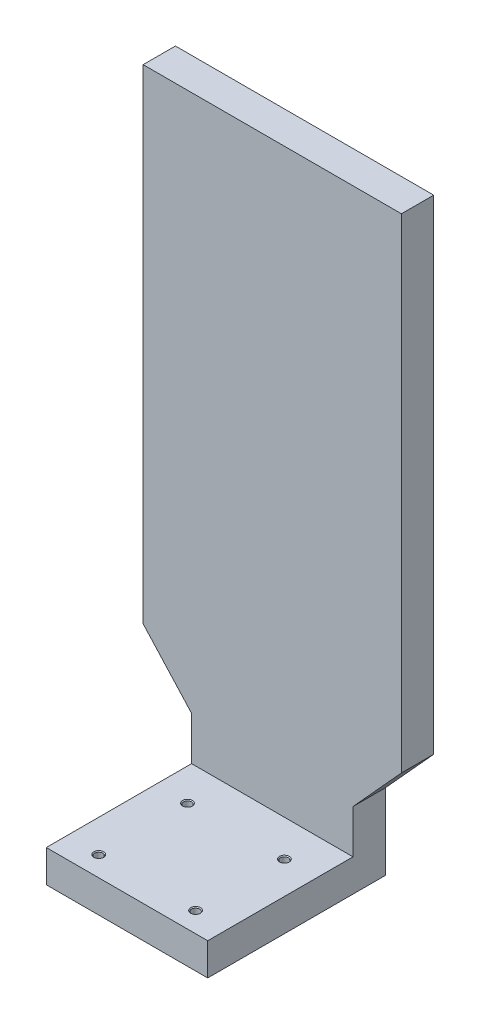
SolidWorks part; units mm, degrees
material "Aluminium"
ref_plane "Ebene vorne" through (0, 0, 0) normal (0, 0, 1) x (1, 0, 0)
ref_plane "Ebene oben" through (0, 0, 0) normal (0, 1, 0) x (1, 0, 0)
ref_plane "Ebene rechts" through (0, 0, 0) normal (1, 0, 0) x (0, 0, -1)
sketch "Skizze1" plane through (0, 0, 0) normal (0, 0, 1) x (1, 0, 0)
  line L0 (80, 0) -> (80, 300) construction
  line L1 (0, 0) -> (160, 0)
  line L2 (0, 0) -> (0, 300)
  line L3 (0, 300) -> (160, 300)
  line L4 (160, 0) -> (160, 300)
  line L5 (80, -33) -> (80, -60) construction
  line L6 (130, -33) -> (160, 0)
  line L7 (30, -33) -> (130, -33)
  line L8 (30, -33) -> (30, -60)
  line L9 (30, -60) -> (130, -60)
  line L10 (130, -33) -> (130, -60)
  line L11 (0, 0) -> (30, -33)
  dimension "D1" = 160
  dimension "D2" = 300
  dimension "D3" = 360
  dimension "D4" = 27
  dimension "D5" = 100
extrude "Aufsatz-Linear austragen1" add sketch "Skizze1" along normal blind 20 contours L1 L4 L3 L2 | L1 L11 L7 L6 | L10 L7 L8 L9
sketch "Skizze2" plane through (0, 0, 20) normal (0, 0, 1) x (1, 0, 0)
  line L0 (130, -33) -> (130, -60) construction
  line L1 (30, -60) -> (130, -60)
  line L2 (30, -60) -> (30, -80)
  line L3 (30, -80) -> (130, -80)
  line L4 (130, -60) -> (130, -80)
  dimension "D1" = 20
extrude "Aufsatz-Linear austragen2" add sketch "Skizze2" along normal blind 90 and the other way up to surface (20 mm away) other way up to face at (80, 51.75, 0)
hole_wizard "M6 Gewindebohrung1" positions "Skizze3" profile "Skizze4" tap size "M6" standard "DIN" end condition through all
sketch "Skizze3" plane through (0, -60, 0) normal (0, 1, 0) x (1, 0, 0)
  line L0 (130, -110) -> (30, -110) construction
  line L1 (80, -20) -> (80, -110) construction
  line L2 (0, -20) -> (160, -20) construction
  line L6 (130, -65) -> (30, -65) construction
  line L7 (130, -20) -> (130, -110) construction
  line L8 (30, -20) -> (30, -110) construction
  point P0 (50, -97.5)
  point P22 (110, -97.5)
  point P24 (110, -42.5)
  point P25 (50, -42.5)
  dimension "D1" = 12.5
  dimension "D2" = 30
  dimension "D3" = 55
sketch "Skizze4" plane through (50, -60, 97.5) normal (1, 0, 0) x (0, 0, 1)
  line L0 (0, 0) -> (0, 20)
  line L1 (0, 20) -> (2.5, 20)
  line L2 (2.5, 20) -> (2.5, 0.525)
  line L3 (2.5, 0.525) -> (3.025, 0)
  line L5 (3.025, 0) -> (0, 0)
  line L6 (-2.5, 0.525) -> (-3.025, 0) construction
  line L11 (0, -6.35) -> (0, 107.95) construction
  dimension "Bohrerdurchmesser" = 5
  dimension "Bohrungstiefe" = 20
  dimension "Senkdurchmesser (Oben)" = 6.05
  dimension "Senkwinkel (Oben)" = 90
cosmetic thread "Bohrungsgewinde1" parameters "D2"=6
cosmetic thread "Bohrungsgewinde2" parameters "D2"=6
cosmetic thread "Bohrungsgewinde3" parameters "D2"=6
cosmetic thread "Bohrungsgewinde4" parameters "D2"=6
